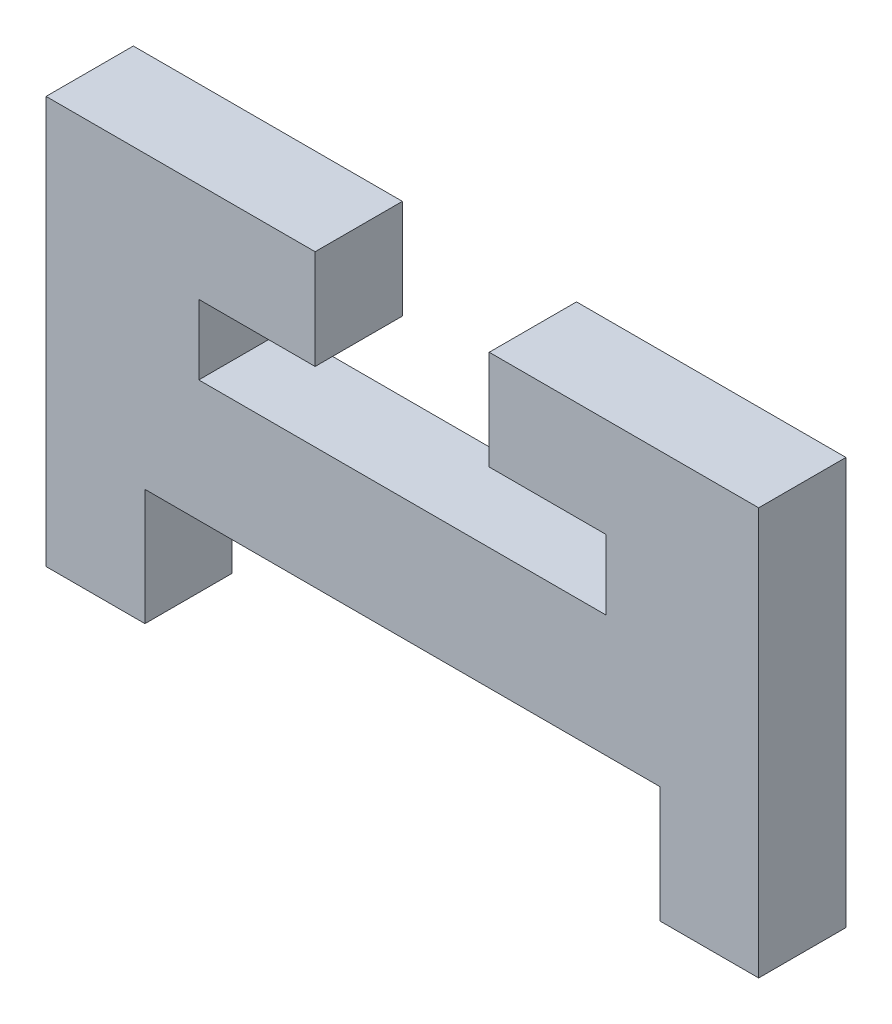
SolidWorks part; units mm, degrees
ref_plane "Alzado" through (0, 0, 0) normal (0, 0, 1) x (1, 0, 0)
ref_plane "Planta" through (0, 0, 0) normal (0, 1, 0) x (1, 0, 0)
ref_plane "Vista lateral" through (0, 0, 0) normal (1, 0, 0) x (0, 0, -1)
sketch "Model" plane through (0, 0, 0) normal (0, 0, 1) x (1, 0, 0)
  line L0 (38.05, 7.7) -> (41.45, 7.7)
  line L1 (41.45, 7.7) -> (41.45, 21.7)
  line L2 (41.45, 21.7) -> (32.1864, 21.7)
  line L3 (32.1864, 21.7) -> (32.1864, 18.2827)
  line L4 (32.1864, 18.2827) -> (36.2, 18.2827)
  line L5 (36.2, 18.2827) -> (36.2, 15.8827)
  line L6 (36.2, 15.8827) -> (29.7, 15.8827)
  line L7 (29.7, 15.8827) -> (22.2, 15.8827)
  line L8 (22.2, 15.8827) -> (22.2, 18.2827)
  line L9 (22.2, 18.2827) -> (26.2, 18.2827)
  line L10 (26.2, 18.2827) -> (26.2, 21.7)
  line L11 (26.2, 21.7) -> (16.95, 21.7)
  line L12 (16.95, 21.7) -> (16.95, 7.7)
  line L13 (16.95, 7.7) -> (20.35, 7.7)
  line L14 (20.35, 7.7) -> (20.35, 11.7)
  line L15 (20.35, 11.7) -> (38.05, 11.7)
  line L16 (38.05, 11.7) -> (38.05, 7.7)
extrude "Saliente-Extruir1" add sketch "Model" along normal blind 3
